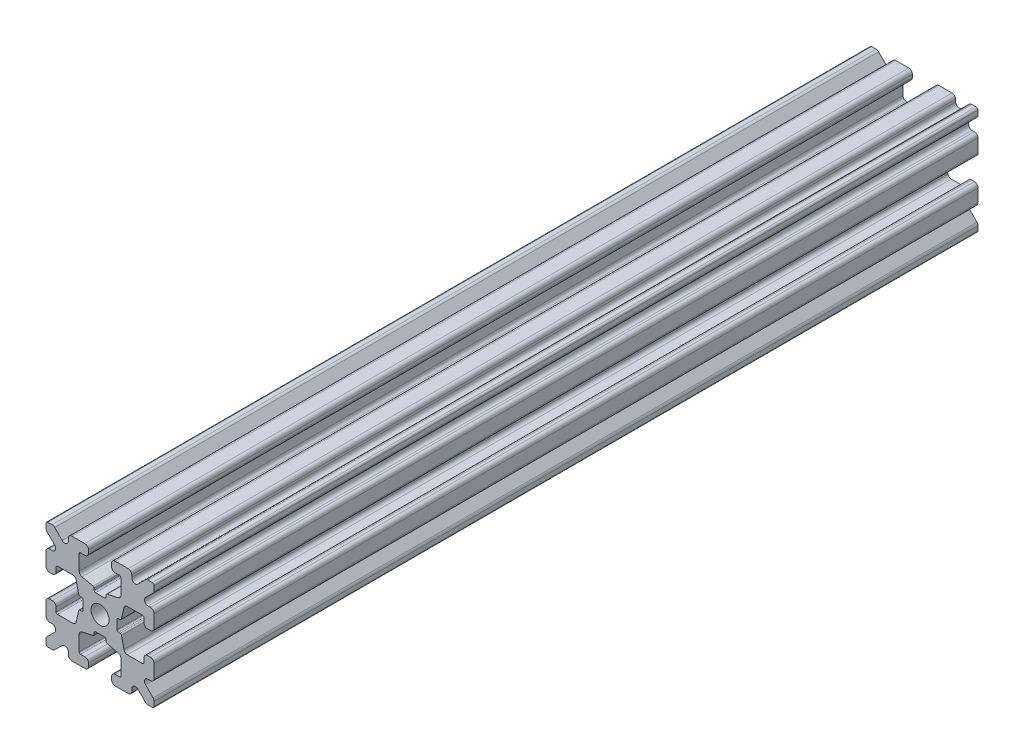
SolidWorks part; units mm, degrees
ref_plane "Front Plane" through (0, 0, 0) normal (0, 0, 1) x (1, 0, 0)
ref_plane "Top Plane" through (0, 0, 0) normal (0, 1, 0) x (1, 0, 0)
ref_plane "Right Plane" through (0, 0, 0) normal (1, 0, 0) x (0, 0, -1)
sketch "Sketch1" plane through (0, 0, 0) normal (0, 0, 1) x (1, 0, 0)
  line L1 (-7.5, -7.5) -> (7.5, -7.5)
  line L2 (-7.5, -7.5) -> (-7.5, 7.5)
  line L3 (-7.5, 7.5) -> (7.5, 7.5)
  line L4 (7.5, -7.5) -> (7.5, 7.5)
  line L5 (-7.5, -7.5) -> (7.5, 7.5) construction
  line L6 (-7.5, 7.5) -> (7.5, -7.5) construction
  circle A0 centre (0, 0) radius 1.25
  point P0 (0, 0)
  dimension "D2" = 2.5
  dimension "D1" = 15
extrude "Boss-Extrude1" add sketch "Sketch1" along normal mid plane 114.3
fillet "Fillet1" radius 0.25 4 edges at (7.5, -7.5, 0) (-7.5, -7.5, 0) (7.5, 7.5, 0) (-7.5, 7.5, 0)
sketch "Sketch2" plane through (0, 0, 57.15) normal (0, 0, 1) x (1, 0, 0)
  line L0 (-7.5, 7.25) -> (-7.5, -7.25) construction
  line L1 (-7.5, 1.6) -> (-6.1, 1.6)
  line L2 (-7.5, 1.6) -> (-7.5, -1.6)
  line L3 (-7.5, -1.6) -> (-6.1, -1.6)
  line L4 (-6.1, 1.6) -> (-6.1, 2.9)
  line L5 (0, 0) -> (-12.1036, 0) construction
  line L6 (-6.1, -2.9) -> (-3.4, -2.9)
  line L7 (0, 0) -> (-7.25, 7.25) construction
  line L8 (-6.1, 2.9) -> (-3.4, 2.9)
  line L9 (-3.4, -2.9) -> (-3.4, 2.9)
  line L10 (55, 0) -> (-55, 0) construction
  line L11 (-6.1, -2.9) -> (-6.1, -1.6)
  line L12 (2.9, 6.1) -> (1.6, 6.1)
  line L13 (2.9, 3.4) -> (-2.9, 3.4)
  line L14 (-2.9, 6.1) -> (-2.9, 3.4)
  line L15 (2.9, 6.1) -> (2.9, 3.4)
  line L16 (-1.6, 6.1) -> (-2.9, 6.1)
  line L17 (1.6, 7.5) -> (1.6, 6.1)
  line L18 (-1.6, 7.5) -> (1.6, 7.5)
  line L19 (-1.6, 7.5) -> (-1.6, 6.1)
  line L20 (-1.6, -7.5) -> (-1.6, -6.1)
  line L21 (-1.6, -7.5) -> (1.6, -7.5)
  line L22 (1.6, -7.5) -> (1.6, -6.1)
  line L23 (-1.6, -6.1) -> (-2.9, -6.1)
  line L24 (2.9, -6.1) -> (2.9, -3.4)
  line L25 (-2.9, -6.1) -> (-2.9, -3.4)
  line L26 (2.9, -3.4) -> (-2.9, -3.4)
  line L27 (2.9, -6.1) -> (1.6, -6.1)
  line L28 (6.1, -2.9) -> (6.1, -1.6)
  line L29 (3.4, -2.9) -> (3.4, 2.9)
  line L30 (6.1, 2.9) -> (3.4, 2.9)
  line L31 (6.1, -2.9) -> (3.4, -2.9)
  line L32 (6.1, 1.6) -> (6.1, 2.9)
  line L33 (7.5, -1.6) -> (6.1, -1.6)
  line L34 (7.5, 1.6) -> (7.5, -1.6)
  line L35 (7.5, 1.6) -> (6.1, 1.6)
  dimension "D1" = 3.2
  dimension "D2" = 5.8
  dimension "D3" = 1.4
  dimension "D4" = 2.7
extrude "Cut-Extrude1" cut sketch "Sketch2" against normal through all
sketch "Sketch4" plane through (0, 0, 57.15) normal (0, 0, 1) x (1, 0, 0)
  line L0 (-3.4, 2.9) -> (-2.75, 0)
  line L1 (55, 0) -> (-55, 0) construction
  line L2 (-2.75, 0) -> (-3.4, -2.9)
  line L3 (-3.4, -2.9) -> (-3.4, 2.9) construction
  line L4 (-3.4, 2.9) -> (-3.4, -2.9)
  line L5 (-2.9, 3.4) -> (0, 2.75)
  line L6 (0, 2.75) -> (2.9, 3.4)
  line L7 (2.9, 3.4) -> (-2.9, 3.4)
  line L8 (3.4, 2.9) -> (2.75, 0)
  line L9 (2.75, 0) -> (3.4, -2.9)
  line L10 (3.4, -2.9) -> (3.4, 2.9)
  line L11 (-2.9, -3.4) -> (0, -2.75)
  line L12 (0, -2.75) -> (2.9, -3.4)
  line L13 (2.9, -3.4) -> (-2.9, -3.4)
  circle A2 centre (0, 0) radius 2.75
  circle A3 centre (0, 0) radius 2.75 construction
  dimension "D1" = 1.5
extrude "Cut-Extrude3" cut sketch "Sketch4" against normal through all
fillet "Fillet3" radius 0.5 16 edges at (-6.1, -1.6, 0) (-7.5, -1.6, 0) (-6.1, 1.6, 0) (-7.5, 1.6, 0) (-1.6, -7.5, 0) (-1.6, -6.1, 0) (1.6, -7.5, 0) (1.6, -6.1, 0) (6.1, -1.6, 0) (7.5, -1.6, 0) (7.5, 1.6, 0) (6.1, 1.6, 0) (1.6, 7.5, 0) (1.6, 6.1, 0) (-1.6, 7.5, 0) (-1.6, 6.1, 0)
fillet "Fillet4" radius 0.5 8 edges at (-3.4, 2.9, 0) (-3.4, -2.9, 0) (2.9, -3.4, 0) (-2.9, -3.4, 0) (3.4, -2.9, 0) (3.4, 2.9, 0) (-2.9, 3.4, 0) (2.9, 3.4, 0)
fillet "Fillet5" radius 3 4 edges at (0, -2.75, 0) (2.75, 0, 0) (-2.75, 0, 0) (0, 2.75, 0)
fillet "Fillet6" radius 0.2 8 edges at (-2.9, -6.1, 0) (2.9, -6.1, 0) (6.1, -2.9, 0) (6.1, 2.9, 0) (2.9, 6.1, 0) (-2.9, 6.1, 0) (-6.1, -2.9, 0) (-6.1, 2.9, 0)
sketch "Sketch5" plane through (0, 0, 57.15) normal (0, 0, 1) x (1, 0, 0)
  line L0 (0, 0) -> (-7.25, 7.25) construction
  line L1 (-7.5, 6.4393) -> (-5.4607, 4.4)
  line L2 (-6.4393, 7.5) -> (-4.4, 5.4607)
  line L3 (-7.5, 4.4) -> (-5.4607, 4.4)
  line L4 (-3.8003, 2.9) -> (-5.9, 2.9) construction
  line L5 (0, 0) -> (-12.1819, 0) construction
  line L6 (-4.4, 7.5) -> (-4.4, 5.4607)
  line L7 (-2.9, 5.9) -> (-2.9, 3.8003) construction
  line L8 (-7.5, 6.4393) -> (-7.5, 4.4)
  line L9 (-7.5, 7.25) -> (-7.5, 2.1) construction
  line L10 (2.1, -7.5) -> (7.25, -7.5) construction
  line L11 (7.5, -7.25) -> (7.5, -2.1) construction
  line L12 (7.25, 7.5) -> (2.1, 7.5) construction
  line L13 (-2.1, 7.5) -> (-7.25, 7.5) construction
  line L14 (-4.4, 7.5) -> (-6.4393, 7.5)
  line L16 (55, 0) -> (-55, 0) construction
  line L17 (0, 0) -> (0, 10.993) construction
  line L18 (0, -54.6431) -> (0, 54.6431) construction
  line L20 (4.4, 7.5) -> (6.4393, 7.5)
  line L22 (7.5, 6.4393) -> (7.5, 4.4)
  line L23 (4.4, 7.5) -> (4.4, 5.4607)
  line L24 (7.5, 4.4) -> (5.4607, 4.4)
  line L25 (6.4393, 7.5) -> (4.4, 5.4607)
  line L26 (7.5, 6.4393) -> (5.4607, 4.4)
  line L27 (7.5, -6.4393) -> (5.4607, -4.4)
  line L28 (6.4393, -7.5) -> (4.4, -5.4607)
  line L29 (7.5, -4.4) -> (5.4607, -4.4)
  line L30 (4.4, -7.5) -> (4.4, -5.4607)
  line L31 (7.5, -6.4393) -> (7.5, -4.4)
  line L33 (4.4, -7.5) -> (6.4393, -7.5)
  line L36 (-4.4, -7.5) -> (-6.4393, -7.5)
  line L38 (-7.5, -6.4393) -> (-7.5, -4.4)
  line L39 (-4.4, -7.5) -> (-4.4, -5.4607)
  line L40 (-7.5, -4.4) -> (-5.4607, -4.4)
  line L41 (-6.4393, -7.5) -> (-4.4, -5.4607)
  line L42 (-7.5, -6.4393) -> (-5.4607, -4.4)
  dimension "D1" = 1.5
  dimension "D2" = 1.5
  dimension "D3" = 1.5
extrude "Cut-Extrude4" cut sketch "Sketch5" against normal through all
fillet "Fillet8" radius 0.5 24 edges at (-5.4607, 4.4, 0) (-7.5, 4.4, 0) (-5.4607, -4.4, 0) (-7.5, -4.4, 0) (-4.4, -7.5, 0) (-4.4, -5.4607, 0) (4.4, -7.5, 0) (4.4, -5.4607, 0) (5.4607, -4.4, 0) (7.5, -4.4, 0) (7.5, 4.4, 0) (5.4607, 4.4, 0) (4.4, 5.4607, 0) (4.4, 7.5, 0) (-4.4, 5.4607, 0) (-4.4, 7.5, 0) (-6.4393, 7.5, 0) (-7.5, 6.4393, 0) (6.4393, 7.5, 0) (7.5, 6.4393, 0) (6.4393, -7.5, 0) (7.5, -6.4393, 0) (-6.4393, -7.5, 0) (-7.5, -6.4393, 0)
sketch "Sketch6" plane through (0, 0, 57.15) normal (0, 0, 1) x (1, 0, 0)
  line L0 (0, 0) -> (0, 11.013) construction
  line L1 (0.6561, 2.8971) -> (2.1235, 2.8971) construction
  line L2 (0, -54.6431) -> (0, 54.6431) construction
  line L3 (0, 0) -> (7.25, 7.25) construction
  line L4 (7.5, 0.8255) -> (7.5, -0.8255)
  line L5 (2.3471, 0.8255) -> (7.5, 0.8255)
  line L6 (0, 0) -> (12.4016, 0) construction
  line L7 (0.8255, -7.5) -> (-0.8255, -7.5)
  line L8 (2.3471, -0.8255) -> (2.3471, 0.8255)
  line L9 (0.8255, -2.3471) -> (0.8255, -7.5)
  line L10 (7.5, -0.8255) -> (2.3471, -0.8255)
  line L11 (-7.5, -0.8255) -> (-2.3471, -0.8255)
  line L12 (-2.3471, -0.8255) -> (-2.3471, 0.8255)
  line L13 (-0.8255, -2.3471) -> (0.8255, -2.3471)
  line L14 (-0.8255, 7.5) -> (-0.8255, 2.3471)
  line L15 (-0.8255, 2.3471) -> (0.8255, 2.3471)
  line L16 (-0.8255, -7.5) -> (-0.8255, -2.3471)
  line L17 (0.8255, 2.3471) -> (0.8255, 7.5)
  line L18 (0.8255, 7.5) -> (-0.8255, 7.5)
  line L19 (3.9, 7.5) -> (2.1, 7.5) construction
  line L20 (-2.3471, 0.8255) -> (-7.5, 0.8255)
  line L21 (-7.5, 0.8255) -> (-7.5, -0.8255)
  point P5 (0, -2.5973)
  point P7 (0, 2.5973)
  dimension "D3" = 0.55
  dimension "D1" = 1.651
extrude "Cut-Extrude5" cut sketch "Sketch6" against normal through all
fillet "Fillet10" radius 0.2 16 edges at (-2.935, 0.8255, 0) (-2.935, -0.8255, 0) (2.935, -0.8255, 0) (2.935, 0.8255, 0) (0.8255, 2.935, 0) (-0.8255, 2.935, 0) (-2.3471, 0.8255, 0) (-2.3471, -0.8255, 0) (0.8255, 2.3471, 0) (-0.8255, 2.3471, 0) (2.3471, 0.8255, 0) (2.3471, -0.8255, 0) (0.8255, -2.935, 0) (0.8255, -2.3471, 0) (-0.8255, -2.3471, 0) (-0.8255, -2.935, 0)
